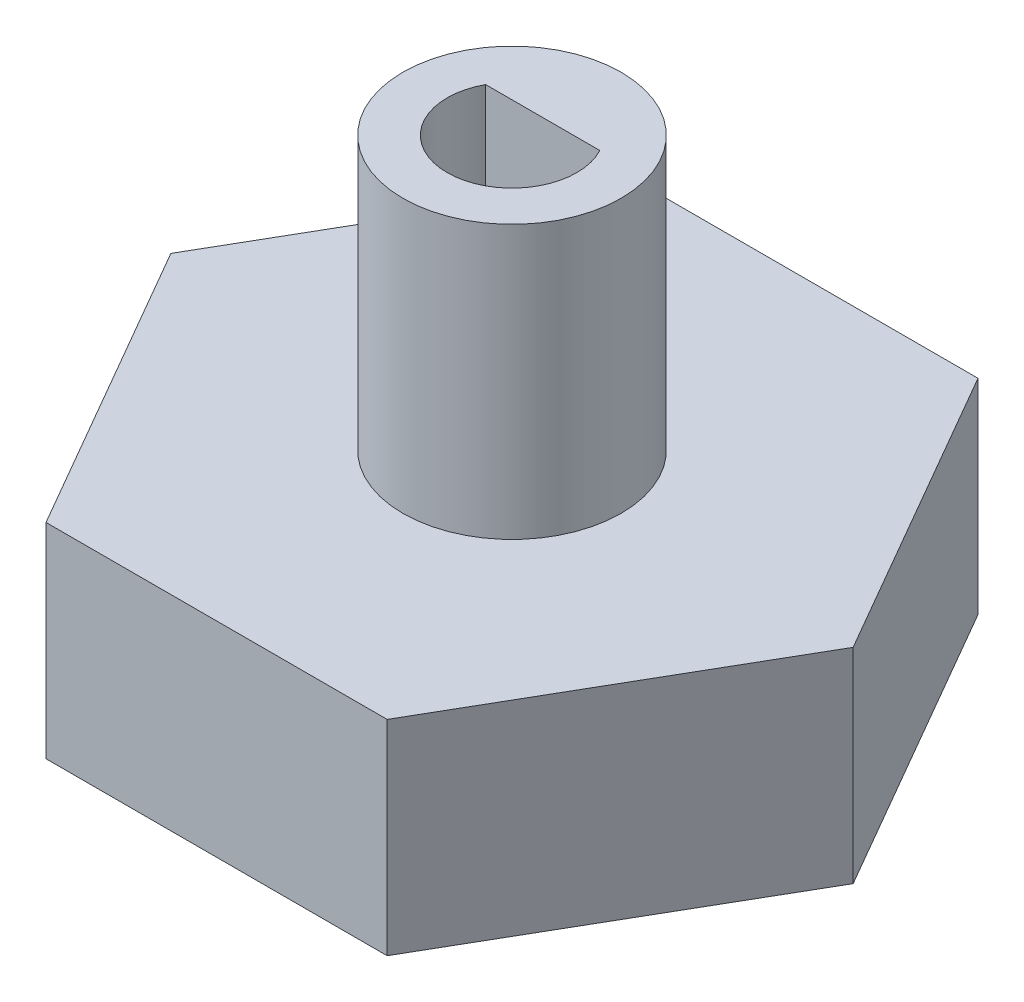
SolidWorks part; units mm, degrees
ref_plane "Front Plane" through (0, 0, 0) normal (0, 0, 1) x (1, 0, 0)
ref_plane "Top Plane" through (0, 0, 0) normal (0, 1, 0) x (1, 0, 0)
ref_plane "Right Plane" through (0, 0, 0) normal (1, 0, 0) x (0, 0, -1)
sketch "Sketch1" plane through (0, 0, 0) normal (0, 1, 0) x (1, 0, 0)
  line L1 (6.35, 0) -> (3.175, 5.4993)
  line L2 (3.175, 5.4993) -> (-3.175, 5.4993)
  line L3 (-3.175, 5.4993) -> (-6.35, 0)
  line L4 (-6.35, 0) -> (-3.175, -5.4993)
  line L5 (-3.175, -5.4993) -> (3.175, -5.4993)
  line L6 (3.175, -5.4993) -> (6.35, 0)
  circle A0 centre (0, 0) radius 5.4993 construction
  dimension "D1" = 12.7
extrude "Boss-Extrude1" add sketch "Sketch1" along normal blind 3.81
sketch "Sketch2" plane through (0, 3.81, 0) normal (0, 1, 0) x (1, 0, 0)
  circle A0 centre (0, 0) radius 2.032
  dimension "D1" = 4.064
extrude "Boss-Extrude2" add sketch "Sketch2" along normal blind 5.08
sketch "Sketch3" plane through (0, 0, 0) normal (0, -1, 0) x (1, 0, 0)
  line L0 (-1.0626, -0.5715) -> (1.0626, -0.5715)
  line L1 (0, 1.2065) -> (0, -0.5715) construction
  arc A0 (1.0626, -0.5715) -> (-1.0626, -0.5715) centre (0, 0) ccw
  dimension "D1" = 2.413
  dimension "D2" = 1.778
extrude "Cut-Extrude1" cut sketch "Sketch3" against normal through all
